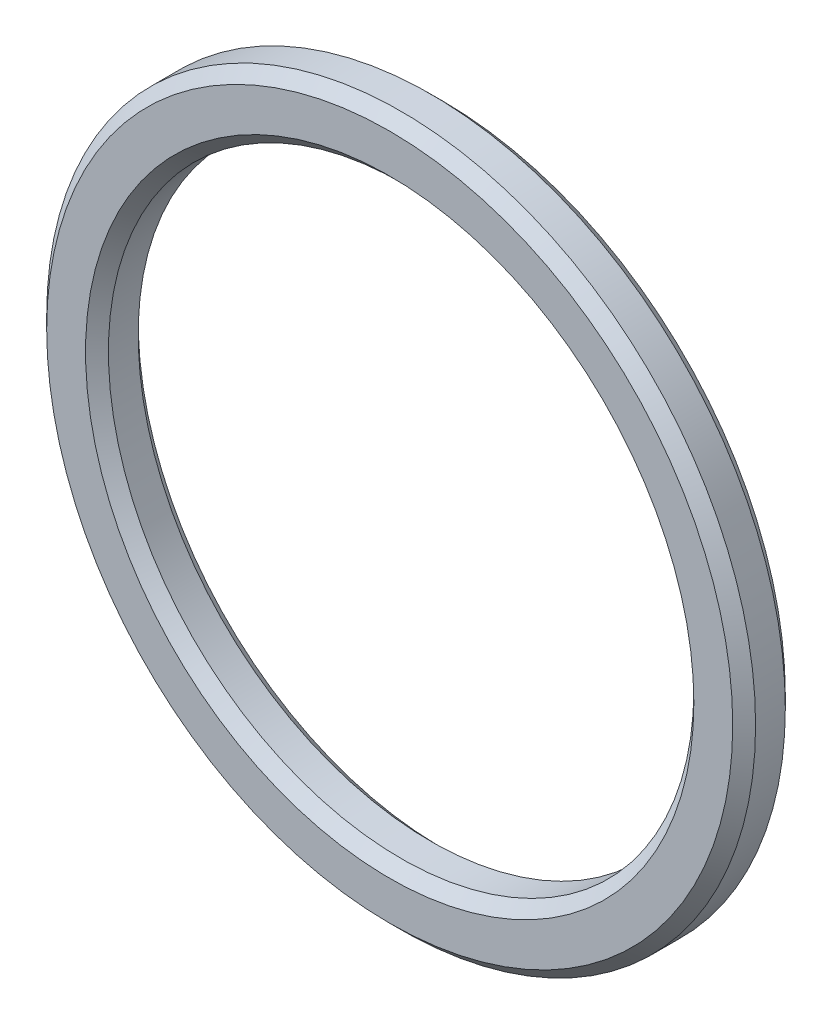
SolidWorks part; units mm, degrees
ref_plane "Front Plane" through (0, 0, 0) normal (0, 0, 1) x (1, 0, 0)
ref_plane "Top Plane" through (0, 0, 0) normal (0, 1, 0) x (1, 0, 0)
ref_plane "Right Plane" through (0, 0, 0) normal (1, 0, 0) x (0, 0, -1)
sketch "Sketch1" plane through (0, 0, 0) normal (0, 0, 1) x (1, 0, 0)
  circle A0 centre (0, 0) radius 12.8
  circle A1 centre (0, 0) radius 15.5
  dimension "D1" = 25.6
  dimension "D2" = 31
extrude "Boss-Extrude1" add sketch "Sketch1" along normal blind 2.3
chamfer "Chamfer1" distance 0.5 angle 45 4 edges at (12.8, 0, 0) (15.5, 0, 0) (12.8, 0, 2.3) (15.5, 0, 2.3)
